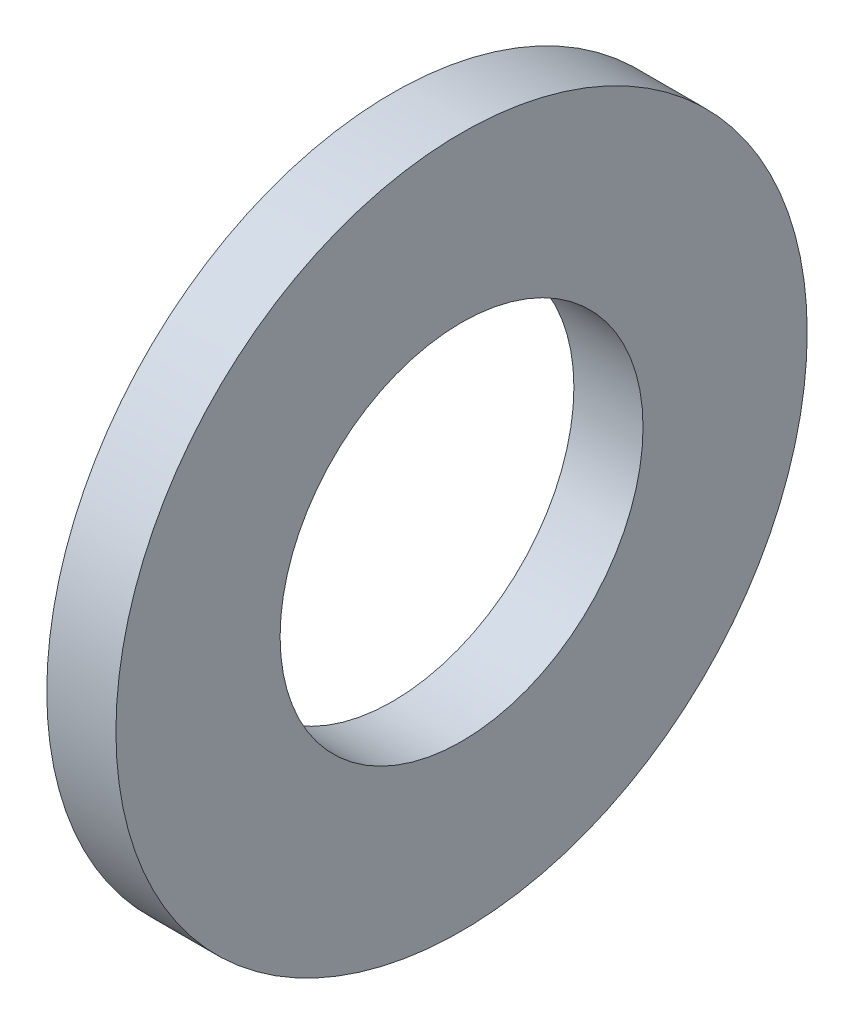
SolidWorks part; units mm, degrees
ref_plane "Płaszczyzna przednia" through (0, 0, 0) normal (0, 0, 1) x (1, 0, 0)
ref_plane "Płaszczyzna górna" through (0, 0, 0) normal (0, 1, 0) x (1, 0, 0)
ref_plane "Płaszczyzna prawa" through (0, 0, 0) normal (1, 0, 0) x (0, 0, -1)
sketch "Szkic1" plane through (0, 0, 0) normal (0, 0, 1) x (1, 0, 0)
  line L0 (0, 8) -> (0, 4.2)
  line L1 (0, 4.2) -> (1.6, 4.2)
  line L2 (1.6, 4.2) -> (1.6, 8)
  line L3 (1.6, 8) -> (0, 8)
  line L4 (0, 0) -> (1.6305, 0) construction
  dimension "D1" = 8
  dimension "D2" = 1.6
  dimension "D3" = 4.2
  dimension "D4" = 1.6305
revolve "Obrót1" add sketch "Szkic1" angle 360 about L4
